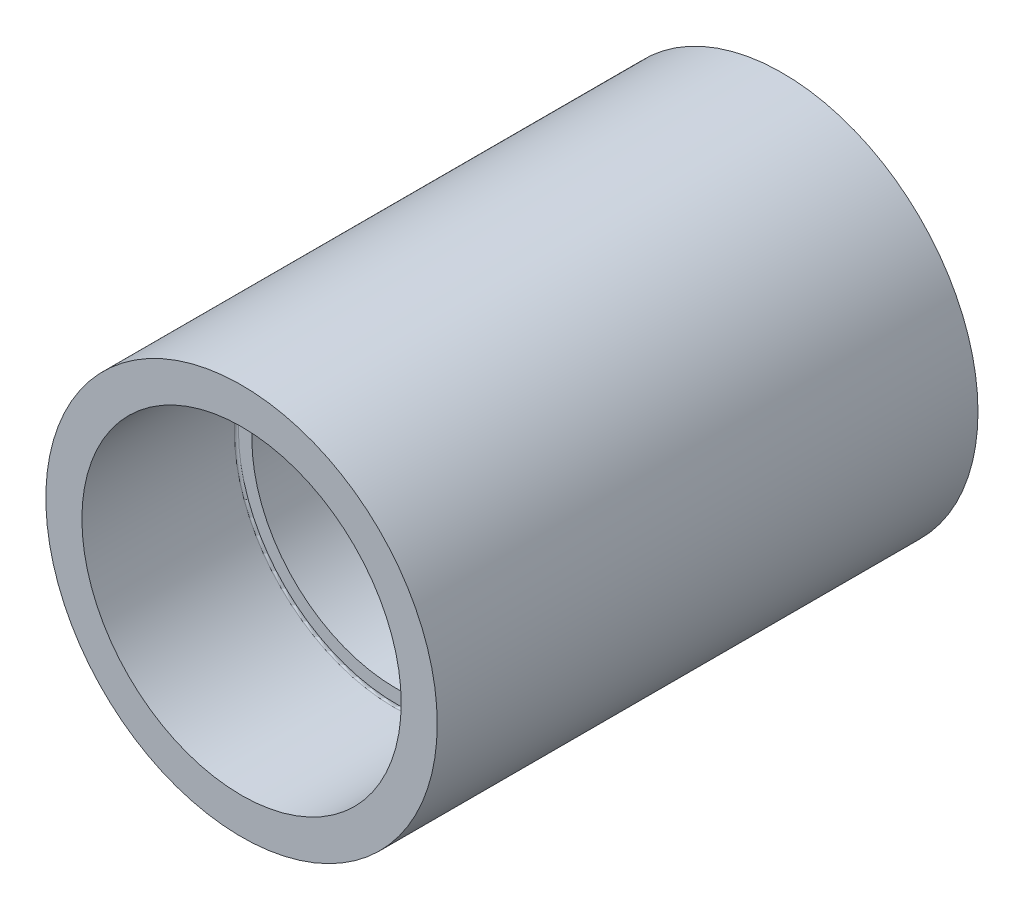
SolidWorks part; units mm, degrees
material "Acier S235"
ref_plane "Plan de face" through (0, 0, 0) normal (0, 0, 1) x (1, 0, 0)
ref_plane "Plan de dessus" through (0, 0, 0) normal (0, 1, 0) x (1, 0, 0)
ref_plane "Plan de droite" through (0, 0, 0) normal (1, 0, 0) x (0, 0, -1)
sketch "Esquisse1" plane through (0, 0, 0) normal (1, 0, 0) x (0, 0, -1)
  line L0 (-52.5, 38) -> (52.5, 38)
  line L1 (52.5, 38) -> (52.5, 31)
  line L2 (52.5, 31) -> (22.5, 31)
  line L3 (22.5, 31) -> (22.5, 28)
  line L4 (22.5, 28) -> (-22.5, 28)
  line L5 (-22.5, 28) -> (-22.5, 31)
  line L6 (-22.5, 31) -> (-52.5, 31)
  line L7 (-52.5, 31) -> (-52.5, 38)
  line L8 (-52.5, 0) -> (52.5, 0) construction
  dimension "D1" = 105
  dimension "D2" = 30
  dimension "D3" = 45
  dimension "D4" = 10
  dimension "D5" = 76
  dimension "D6" = 62
revolve "Révolution1" add sketch "Esquisse1" angle 360 about L8
fillet "Congé1" radius 0.4 2 edges at (31, 0, -22.5) (31, 0, 22.5)
ref_plane "Plan1" through (0, 38, 0) normal (0, 1, 0) x (1, 0, 0)
chamfer "Chanfrein1" [suppressed] distance 2 angle 45
